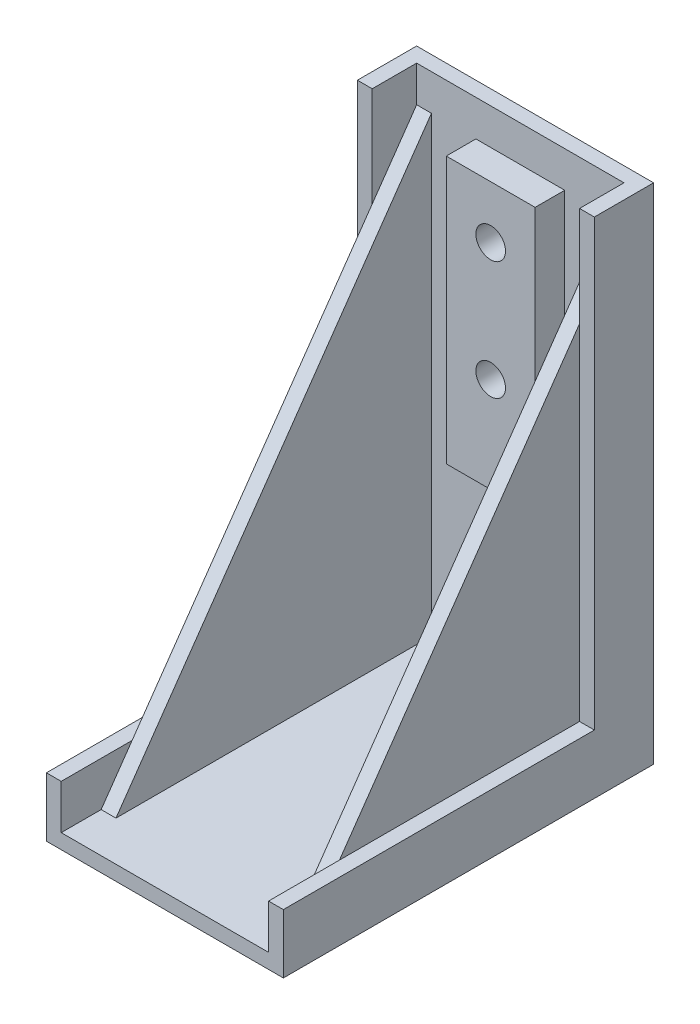
SolidWorks part; units mm, degrees
ref_plane "Front Plane" through (0, 0, 0) normal (0, 0, 1) x (1, 0, 0)
ref_plane "Top Plane" through (0, 0, 0) normal (0, 1, 0) x (1, 0, 0)
ref_plane "Right Plane" through (0, 0, 0) normal (1, 0, 0) x (0, 0, -1)
sketch "Sketch1" plane through (0, 0, 0) normal (1, 0, 0) x (0, 0, -1)
  line L0 (0, 0) -> (31.25, 0)
  line L1 (31.25, 0) -> (31.25, 42.5)
  line L3 (31.25, 42.5) -> (26.25, 42.5)
  line L4 (26.25, 42.5) -> (26.25, 5)
  line L5 (26.25, 5) -> (0, 5)
  line L6 (0, 5) -> (0, 0)
  dimension "D1" = 31.25
  dimension "D2" = 42.5
  dimension "D3" = 5
  dimension "D4" = 5
extrude "Boss-Extrude1" add sketch "Sketch1" along normal mid plane 20
shell "Shell1" thickness 1.25
sketch "Sketch4" plane through (-8.75, 0, 0) normal (1, 0, 0) x (0, 0, -1)
  line L0 (2.5, 0) -> (31.25, 41.25)
  line L1 (31.25, 0) -> (31.25, 42.5) construction
  line L2 (0, 0) -> (31.25, 0) construction
  line L3 (0, 0) -> (31.25, 0) construction
  point P6 (31.3239, 41.25)
  point P7 (0, 0)
  point P8 (0, 0)
  dimension "D1" = 28.75
  dimension "D2" = 41.25
rib "Rib1" sketch "Sketch4" sketch "Sketch4" thickness 1.25 parameters "D1"=1.25
mirror "Mirror1" about plane through (0, 0, 0) normal (1, 0, 0) of "Rib1"
sketch "Sketch5" plane through (0, 0, -30) normal (0, 0, 1) x (1, 0, 0)
  line L1 (-3.75, 39.4565) -> (3.75, 39.4565)
  line L2 (-3.75, 39.4565) -> (-3.75, 16.9565)
  line L3 (-3.75, 16.9565) -> (3.75, 16.9565)
  line L4 (3.75, 39.4565) -> (3.75, 16.9565)
  line L5 (8.75, 39.4565) -> (7.5, 39.4565) construction
  point P7 (0, 16.9565)
  point P12 (0, 0)
  point P15 (0, 0)
  dimension "D1" = 7.5
  dimension "D2" = 22.5
extrude "Boss-Extrude2" add sketch "Sketch5" along normal blind 2.5
sketch "Sketch6" plane through (0, 0, -27.5) normal (0, 0, 1) x (1, 0, 0)
  line L0 (8.75, 42.5) -> (-8.75, 42.5) construction
  circle A0 centre (0, 35) radius 1.25
  circle A1 centre (0, 25) radius 1.25
  point P4 (0, 0)
  point P5 (0, 0)
  point P7 (0, 0)
  dimension "D1" = 7.5
  dimension "D3" = 2.5
  dimension "D2" = 10
extrude "Cut-Extrude1" cut sketch "Sketch6" against normal through all
